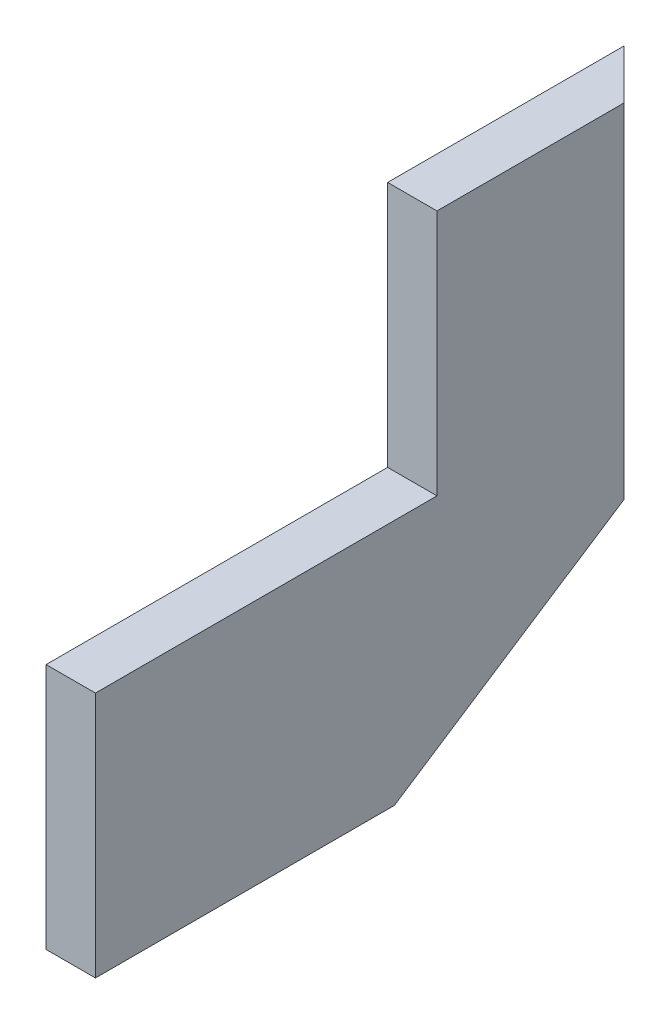
SolidWorks part; units mm, degrees
ref_plane "Front Plane" through (0, 0, 0) normal (0, 0, 1) x (1, 0, 0)
ref_plane "Top Plane" through (0, 0, 0) normal (0, 1, 0) x (1, 0, 0)
ref_plane "Right Plane" through (0, 0, 0) normal (1, 0, 0) x (0, 0, -1)
sketch "Sketch1" plane through (0, 0, 0) normal (1, 0, 0) x (0, 0, -1)
  line L0 (230.7901, 0) -> (446.0575, 140.7778)
  line L6 (0, 0) -> (0, 190.5)
  line L7 (0, 190.5) -> (263.652, 190.5)
  line L8 (446.0575, 381) -> (446.0575, 140.7778)
  line L10 (263.652, 190.5) -> (263.652, 381)
  line L11 (263.652, 381) -> (446.0575, 381)
  line L21 (446.0575, 381) -> (263.652, 381)
  line L25 (263.652, 190.5) -> (241.3, 190.5)
  line L26 (263.652, 190.5) -> (263.652, 381)
  line L29 (241.3, 190.5) -> (0, 190.5)
  line L34 (0, 0) -> (0, 190.5)
  line L41 (0, 0) -> (230.7901, 0)
  line L42 (0, 0) -> (0, 190.5)
  line L43 (0, 190.5) -> (263.652, 190.5)
  dimension "D2" = 190.5
  dimension "D3" = 190.5
  dimension "D4" = 263.652
  dimension "D5" = 240.2222
  dimension "D6" = 182.4055
  dimension "D10" = 285.75
  dimension "D12" = 141.4479
  dimension "D13" = 230.7901
extrude "Boss-Extrude2" add sketch "Sketch1" along normal blind 38.1
sketch "Sketch2" plane through (0, 381, 0) normal (0, 1, 0) x (1, 0, 0)
  line L0 (0, 446.0575) -> (38.1, 407.9575)
  line L2 (38.1, 263.652) -> (38.1, 446.0575) construction
  line L3 (38.1, 407.9575) -> (38.1, 446.0575)
  line L4 (38.1, 446.0575) -> (0, 446.0575)
extrude "Cut-Extrude1" cut sketch "Sketch2" against normal up to next
